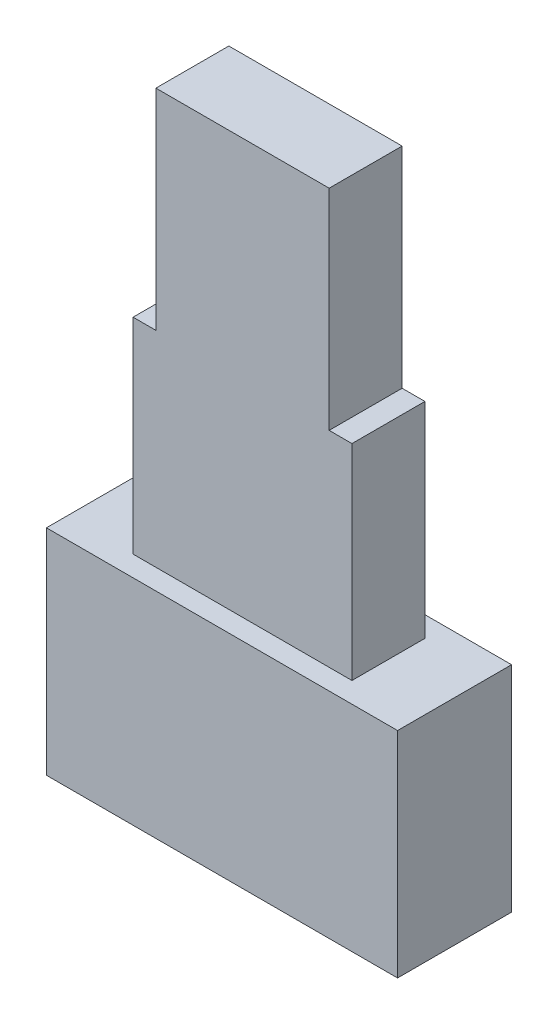
SolidWorks part; units mm, degrees
ref_plane "Спереди" through (0, 0, 0) normal (0, 0, 1) x (1, 0, 0)
ref_plane "Сверху" through (0, 0, 0) normal (0, 1, 0) x (1, 0, 0)
ref_plane "Справа" through (0, 0, 0) normal (1, 0, 0) x (0, 0, -1)
sketch "Sketch1" plane through (0, 0, 0) normal (0, 1, 0) x (1, 0, 0)
  line L1 (3.85, -1.25) -> (-3.85, -1.25)
  line L2 (3.85, -1.25) -> (3.85, 1.25)
  line L3 (3.85, 1.25) -> (-3.85, 1.25)
  line L4 (-3.85, -1.25) -> (-3.85, 1.25)
  line L5 (3.85, -1.25) -> (-3.85, 1.25) construction
  line L6 (3.85, 1.25) -> (-3.85, -1.25) construction
  point P0 (0, 0)
  dimension "D1" = 7.7
  dimension "D2" = 2.5
extrude "Boss-Extrude1" add sketch "Sketch1" along normal blind 4.7
sketch "Sketch2" plane through (0, 4.7, 0) normal (0, 1, 0) x (1, 0, 0)
  line L1 (2.4, -0.8) -> (-2.4, -0.8)
  line L2 (2.4, -0.8) -> (2.4, 0.8)
  line L3 (2.4, 0.8) -> (-2.4, 0.8)
  line L4 (-2.4, -0.8) -> (-2.4, 0.8)
  line L5 (2.4, -0.8) -> (-2.4, 0.8) construction
  line L6 (2.4, 0.8) -> (-2.4, -0.8) construction
  point P0 (0, 0)
  dimension "D1" = 4.8
  dimension "D2" = 1.6
extrude "Boss-Extrude2" add sketch "Sketch2" along normal blind 4.5
sketch "Sketch3" plane through (0, 9.2, 0) normal (0, 1, 0) x (1, 0, 0)
  line L0 (-2.4, -0.8) -> (2.4, -0.8) construction
  line L1 (1.9, -0.8) -> (-1.9, -0.8)
  line L2 (1.9, -0.8) -> (1.9, 0.8)
  line L3 (1.9, 0.8) -> (-1.9, 0.8)
  line L4 (-1.9, -0.8) -> (-1.9, 0.8)
  line L5 (1.9, -0.8) -> (-1.9, 0.8) construction
  line L6 (1.9, 0.8) -> (-1.9, -0.8) construction
  point P0 (0, 0)
  dimension "D1" = 3.8
extrude "Boss-Extrude3" add sketch "Sketch3" along normal blind 4.6
